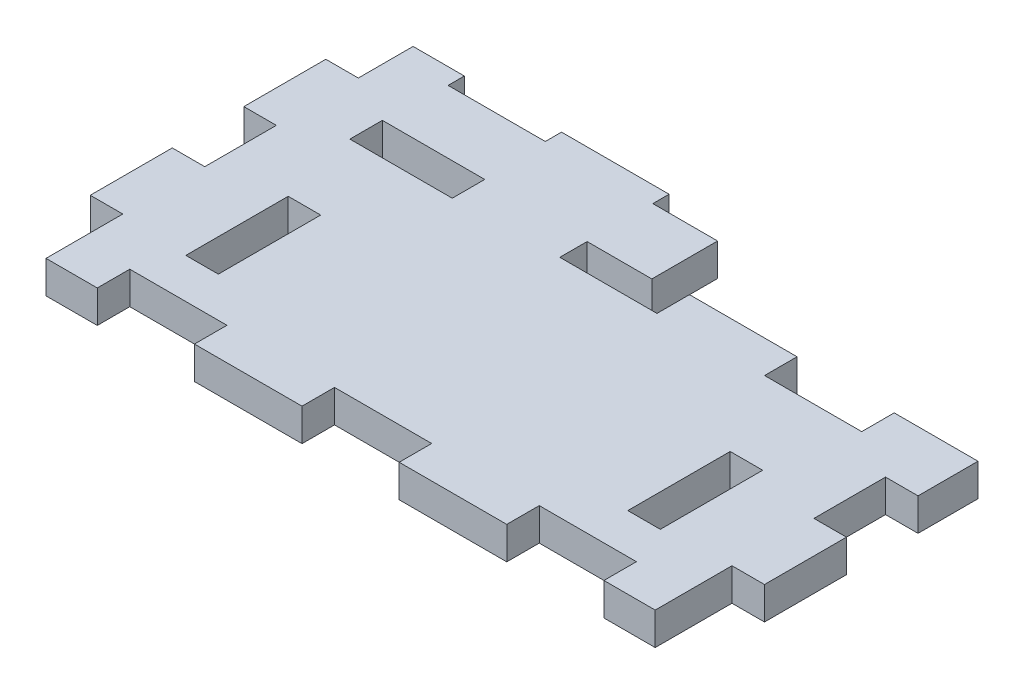
SolidWorks part; units mm, degrees
ref_plane "Front Plane" through (0, 0, 0) normal (0, 0, 1) x (1, 0, 0)
ref_plane "Top Plane" through (0, 0, 0) normal (0, 1, 0) x (1, 0, 0)
ref_plane "Right Plane" through (0, 0, 0) normal (1, 0, 0) x (0, 0, -1)
sketch "Sketch1" plane through (0, 0, 0) normal (0, 1, 0) x (1, 0, 0)
  line L1 (0, 0) -> (65.35, 0)
  line L2 (0, 0) -> (0, 35.35)
  line L3 (0, 35.35) -> (65.35, 35.35)
  line L4 (65.35, 0) -> (65.35, 35.35)
  dimension "D1" = 65.35
  dimension "D2" = 35.35
extrude "Boss-Extrude1" add sketch "Sketch1" along normal blind 3.175
sketch "Sketch2" plane through (0, 0, 0) normal (0, -1, 0) x (1, 0, 0)
  line L0 (65.35, -35.35) -> (0, -35.35) construction
  line L1 (65.35, -35.35) -> (37.175, -35.35)
  line L2 (65.35, -35.35) -> (65.35, -27.85)
  line L3 (65.35, -27.85) -> (37.175, -27.85)
  line L4 (37.175, -35.35) -> (37.175, -27.85)
  line L5 (65.35, 0) -> (65.35, -35.35) construction
  dimension "D1" = 7.5
  dimension "D2" = 28.175
extrude "Cut-Extrude1" cut sketch "Sketch2" against normal through all
sketch "Sketch3" plane through (0, 0, 0) normal (0, -1, 0) x (1, 0, 0)
  line L0 (0, 0) -> (65.35, 0) construction
  line L1 (62.175, -7.5) -> (65.35, -7.5)
  line L2 (62.175, -7.5) -> (62.175, 0)
  line L3 (62.175, 0) -> (65.35, 0)
  line L4 (65.35, -7.5) -> (65.35, 0)
  line L5 (0, -35.35) -> (0, 0) construction
  line L6 (57.675, -3.175) -> (47.675, -3.175)
  line L7 (57.675, -3.175) -> (57.675, 0)
  line L8 (57.675, 0) -> (47.675, 0)
  line L9 (47.675, -3.175) -> (47.675, 0)
  line L10 (37.675, -3.175) -> (27.675, -3.175)
  line L11 (37.675, -3.175) -> (37.675, 0)
  line L12 (37.675, 0) -> (27.675, 0)
  line L13 (27.675, -3.175) -> (27.675, 0)
  line L14 (17.675, -3.175) -> (7.675, -3.175)
  line L15 (17.675, -3.175) -> (17.675, 0)
  line L16 (17.675, 0) -> (7.675, 0)
  line L17 (7.675, -3.175) -> (7.675, 0)
  line L18 (3.175, -7.5) -> (0, -7.5)
  line L19 (3.175, -7.5) -> (3.175, 0)
  line L20 (3.175, 0) -> (0, 0)
  line L21 (0, -7.5) -> (0, 0)
  line L22 (37.175, -35.35) -> (0, -35.35) construction
  line L23 (3.175, -15) -> (0, -15)
  line L24 (3.175, -15) -> (3.175, -22.5)
  line L25 (3.175, -22.5) -> (0, -22.5)
  line L26 (0, -15) -> (0, -22.5)
  line L27 (3.175, -30) -> (0, -30)
  line L28 (3.175, -30) -> (3.175, -35.35)
  line L29 (3.175, -35.35) -> (0, -35.35)
  line L30 (0, -30) -> (0, -35.35)
  line L31 (7.675, -33.7625) -> (17.675, -33.7625)
  line L32 (7.675, -33.7625) -> (7.675, -35.35)
  line L33 (7.675, -35.35) -> (17.675, -35.35)
  line L34 (17.675, -33.7625) -> (17.675, -35.35)
  line L35 (65.35, -27.85) -> (37.175, -27.85) construction
  line L36 (17.675, -27.85) -> (7.675, -27.85)
  line L37 (17.675, -27.85) -> (17.675, -24.675)
  line L38 (17.675, -24.675) -> (7.675, -24.675)
  line L39 (7.675, -27.85) -> (7.675, -24.675)
  line L40 (27.675, -27.85) -> (37.675, -27.85)
  line L41 (27.675, -27.85) -> (27.675, -24.675)
  line L42 (27.675, -24.675) -> (37.675, -24.675)
  line L43 (37.675, -27.85) -> (37.675, -24.675)
  line L44 (34, -27.85) -> (37.175, -27.85)
  line L45 (34, -27.85) -> (34, -33.7625)
  line L46 (34, -33.7625) -> (37.175, -33.7625)
  line L47 (37.175, -27.85) -> (37.175, -33.7625)
  line L48 (27.675, -33.7625) -> (37.175, -33.7625)
  line L49 (27.675, -33.7625) -> (27.675, -35.35)
  line L50 (27.675, -35.35) -> (37.175, -35.35)
  line L51 (37.175, -33.7625) -> (37.175, -35.35)
  line L52 (47.675, -24.675) -> (57.675, -24.675)
  line L53 (47.675, -24.675) -> (47.675, -27.85)
  line L54 (47.675, -27.85) -> (57.675, -27.85)
  line L55 (57.675, -24.675) -> (57.675, -27.85)
  line L56 (65.35, 0) -> (65.35, -27.85) construction
  line L57 (62.175, -22.5) -> (65.35, -22.5)
  line L58 (62.175, -22.5) -> (62.175, -15)
  line L59 (62.175, -15) -> (65.35, -15)
  line L60 (65.35, -22.5) -> (65.35, -15)
  line L62 (37.175, -27.85) -> (37.175, -35.35) construction
  line M40 (37.175, -35.35) -> (37.175, -27.85)
  line M41 (37.175, -27.85) -> (65.35, -27.85)
  line M42 (65.35, -27.85) -> (65.35, 0)
  line M43 (65.35, 0) -> (0, 0)
  line M44 (0, 0) -> (0, -35.35)
  line M45 (0, -35.35) -> (37.175, -35.35)
  dimension "D1" = 10
  dimension "D2" = 10
  dimension "D3" = 10
  dimension "D4" = 10
  dimension "D5" = 10
  dimension "D6" = 4.5
  dimension "D7" = 3.175
  dimension "D8" = 7.5
  dimension "D9" = 7.5
  dimension "D10" = 5.35
  dimension "D11" = 7.5
  dimension "D12" = 7.5
  dimension "D13" = 5.9125
  dimension "D14" = 1.5875
extrude "Cut-Extrude2" cut sketch "Sketch3" against normal blind 3.175 contours L9 L6 L7 M43 | L2 L1 M42 M43 | L59 L58 L57 M42 | L55 L52 L53 M41 | L43 L42 L41 L40 M41 | L45 L46 L40 M40 | L48 L49 L46 M45 M40 | L39 L36 L37 L38 | L28 L27 M44 M45 | L25 L24 L23 M44 | L18 L19 M43 M44 | L17 L14 L15 M43 | L13 L10 L11 M43 | L33 L34 L31 L32
sketch "Sketch7" plane through (0, 0, 0) normal (0, -1, 0) x (1, 0, 0)
  line L1 (9.5, -16.825) -> (12.675, -16.825)
  line L2 (9.5, -16.825) -> (9.5, -6.825)
  line L3 (9.5, -6.825) -> (12.675, -6.825)
  line L4 (12.675, -16.825) -> (12.675, -6.825)
  line L5 (52.675, -16.825) -> (55.85, -16.825)
  line L6 (52.675, -16.825) -> (52.675, -6.825)
  line L7 (52.675, -6.825) -> (55.85, -6.825)
  line L8 (55.85, -16.825) -> (55.85, -6.825)
extrude "Cut-Extrude3" cut sketch "Sketch7" against normal through all
sketch "Sketch6" plane through (0, 3.175, 0) normal (0, 1, 0) x (1, 0, 0)
  line L60 (17.421, 27.596) -> (7.929, 27.596)
  line L61 (7.929, 27.596) -> (7.929, 24.929)
  line L62 (7.929, 24.929) -> (17.421, 24.929)
  line L63 (17.421, 24.929) -> (17.421, 27.596)
  line L64 (17.421, 27.596) -> (7.929, 27.596)
  line L65 (7.929, 27.596) -> (7.929, 24.929)
  line L66 (7.929, 24.929) -> (17.421, 24.929)
  line L67 (17.421, 24.929) -> (17.421, 27.596)
  line L92 (7.929, -0.254) -> (7.929, 2.921)
  line L93 (7.929, 2.921) -> (17.421, 2.921)
  line L94 (17.421, 2.921) -> (17.421, -0.254)
  line L95 (17.421, -0.254) -> (27.929, -0.254)
  line L96 (27.929, -0.254) -> (27.929, 2.921)
  line L97 (27.929, 2.921) -> (37.421, 2.921)
  line L98 (37.421, 2.921) -> (37.421, -0.254)
  line L99 (37.421, -0.254) -> (47.929, -0.254)
  line L100 (47.929, -0.254) -> (47.929, 2.921)
  line L101 (47.929, 2.921) -> (57.421, 2.921)
  line L102 (57.421, 2.921) -> (57.421, -0.254)
  line L103 (57.421, -0.254) -> (62.429, -0.254)
  line L104 (62.429, -0.254) -> (62.429, 7.246)
  line L105 (62.429, 7.246) -> (65.604, 7.246)
  line L106 (65.604, 7.246) -> (65.604, 15.254)
  line L107 (65.604, 15.254) -> (62.429, 15.254)
  line L108 (62.429, 15.254) -> (62.429, 22.246)
  line L109 (62.429, 22.246) -> (65.604, 22.246)
  line L110 (65.604, 22.246) -> (65.604, 28.104)
  line L111 (65.604, 28.104) -> (57.421, 28.104)
  line L112 (57.421, 28.104) -> (57.421, 24.929)
  line L113 (57.421, 24.929) -> (47.929, 24.929)
  line L114 (47.929, 24.929) -> (47.929, 28.104)
  line L115 (47.929, 28.104) -> (37.421, 28.104)
  line L116 (37.421, 28.104) -> (37.421, 24.929)
  line L117 (37.421, 24.929) -> (27.929, 24.929)
  line L118 (27.929, 24.929) -> (27.929, 27.596)
  line L119 (27.929, 27.596) -> (34.254, 27.596)
  line L120 (34.254, 27.596) -> (34.254, 34.0165)
  line L121 (34.254, 34.0165) -> (27.929, 34.0165)
  line L122 (27.929, 34.0165) -> (27.929, 35.604)
  line L123 (27.929, 35.604) -> (17.421, 35.604)
  line L124 (17.421, 35.604) -> (17.421, 34.0165)
  line L125 (17.421, 34.0165) -> (7.929, 34.0165)
  line L126 (7.929, 34.0165) -> (7.929, 35.604)
  line L127 (7.929, 35.604) -> (2.921, 35.604)
  line L128 (2.921, 35.604) -> (2.921, 30.254)
  line L129 (2.921, 30.254) -> (-0.254, 30.254)
  line L130 (-0.254, 30.254) -> (-0.254, 22.246)
  line L131 (-0.254, 22.246) -> (2.921, 22.246)
  line L132 (2.921, 22.246) -> (2.921, 15.254)
  line L133 (2.921, 15.254) -> (-0.254, 15.254)
  line L134 (-0.254, 15.254) -> (-0.254, 7.246)
  line L135 (-0.254, 7.246) -> (2.921, 7.246)
  line L136 (2.921, 7.246) -> (2.921, -0.254)
  line L137 (2.921, -0.254) -> (7.929, -0.254)
  line L138 (7.929, -0.254) -> (7.929, 2.921)
  line L139 (7.929, 2.921) -> (17.421, 2.921)
  line L140 (17.421, 2.921) -> (17.421, -0.254)
  line L141 (17.421, -0.254) -> (27.929, -0.254)
  line L142 (27.929, -0.254) -> (27.929, 2.921)
  line L143 (27.929, 2.921) -> (37.421, 2.921)
  line L144 (37.421, 2.921) -> (37.421, -0.254)
  line L145 (37.421, -0.254) -> (47.929, -0.254)
  line L146 (47.929, -0.254) -> (47.929, 2.921)
  line L147 (47.929, 2.921) -> (57.421, 2.921)
  line L148 (57.421, 2.921) -> (57.421, -0.254)
  line L149 (57.421, -0.254) -> (62.429, -0.254)
  line L150 (62.429, -0.254) -> (62.429, 7.246)
  line L151 (62.429, 7.246) -> (65.604, 7.246)
  line L152 (65.604, 7.246) -> (65.604, 15.254)
  line L153 (65.604, 15.254) -> (62.429, 15.254)
  line L154 (62.429, 15.254) -> (62.429, 22.246)
  line L155 (62.429, 22.246) -> (65.604, 22.246)
  line L156 (65.604, 22.246) -> (65.604, 28.104)
  line L157 (65.604, 28.104) -> (57.421, 28.104)
  line L158 (57.421, 28.104) -> (57.421, 24.929)
  line L159 (57.421, 24.929) -> (47.929, 24.929)
  line L160 (47.929, 24.929) -> (47.929, 28.104)
  line L161 (47.929, 28.104) -> (37.421, 28.104)
  line L162 (37.421, 28.104) -> (37.421, 24.929)
  line L163 (37.421, 24.929) -> (27.929, 24.929)
  line L164 (27.929, 24.929) -> (27.929, 27.596)
  line L165 (27.929, 27.596) -> (34.254, 27.596)
  line L166 (34.254, 27.596) -> (34.254, 34.0165)
  line L167 (34.254, 34.0165) -> (27.929, 34.0165)
  line L168 (27.929, 34.0165) -> (27.929, 35.604)
  line L169 (27.929, 35.604) -> (17.421, 35.604)
  line L170 (17.421, 35.604) -> (17.421, 34.0165)
  line L171 (17.421, 34.0165) -> (7.929, 34.0165)
  line L172 (7.929, 34.0165) -> (7.929, 35.604)
  line L173 (7.929, 35.604) -> (2.921, 35.604)
  line L174 (2.921, 35.604) -> (2.921, 30.254)
  line L175 (2.921, 30.254) -> (-0.254, 30.254)
  line L176 (-0.254, 30.254) -> (-0.254, 22.246)
  line L177 (-0.254, 22.246) -> (2.921, 22.246)
  line L178 (2.921, 22.246) -> (2.921, 15.254)
  line L179 (2.921, 15.254) -> (-0.254, 15.254)
  line L180 (-0.254, 15.254) -> (-0.254, 7.246)
  line L181 (-0.254, 7.246) -> (2.921, 7.246)
  line L182 (2.921, 7.246) -> (2.921, -0.254)
  line L183 (2.921, -0.254) -> (7.929, -0.254)
  line L192 (6.675, 4.175) -> (18.675, 4.175)
  line L193 (6.675, 1) -> (6.675, 4.175)
  line L194 (4.175, 1) -> (6.675, 1)
  line L195 (4.175, 8.5) -> (4.175, 1)
  line L196 (1, 8.5) -> (4.175, 8.5)
  line L197 (1, 14) -> (1, 8.5)
  line L198 (4.175, 14) -> (1, 14)
  line L199 (4.175, 23.5) -> (4.175, 14)
  line L200 (1, 23.5) -> (4.175, 23.5)
  line L201 (1, 29) -> (1, 23.5)
  line L202 (4.175, 29) -> (1, 29)
  line L203 (4.175, 34.35) -> (4.175, 29)
  line L204 (6.675, 34.35) -> (4.175, 34.35)
  line L205 (6.675, 32.7625) -> (6.675, 34.35)
  line L206 (18.675, 32.7625) -> (6.675, 32.7625)
  line L207 (18.675, 34.35) -> (18.675, 32.7625)
  line L208 (26.675, 34.35) -> (18.675, 34.35)
  line L209 (26.675, 32.7625) -> (26.675, 34.35)
  line L210 (33, 32.7625) -> (26.675, 32.7625)
  line L211 (33, 28.85) -> (33, 32.7625)
  line L212 (26.675, 28.85) -> (33, 28.85)
  line L213 (26.675, 23.675) -> (26.675, 28.85)
  line L214 (38.675, 23.675) -> (26.675, 23.675)
  line L215 (38.675, 26.85) -> (38.675, 23.675)
  line L216 (46.675, 26.85) -> (38.675, 26.85)
  line L217 (46.675, 23.675) -> (46.675, 26.85)
  line L218 (58.675, 23.675) -> (46.675, 23.675)
  line L219 (58.675, 26.85) -> (58.675, 23.675)
  line L220 (64.35, 26.85) -> (58.675, 26.85)
  line L221 (64.35, 23.5) -> (64.35, 26.85)
  line L222 (61.175, 23.5) -> (64.35, 23.5)
  line L223 (61.175, 14) -> (61.175, 23.5)
  line L224 (64.35, 14) -> (61.175, 14)
  line L225 (64.35, 8.5) -> (64.35, 14)
  line L226 (61.175, 8.5) -> (64.35, 8.5)
  line L227 (61.175, 1) -> (61.175, 8.5)
  line L228 (58.675, 1) -> (61.175, 1)
  line L229 (58.675, 4.175) -> (58.675, 1)
  line L230 (46.675, 4.175) -> (58.675, 4.175)
  line L231 (46.675, 1) -> (46.675, 4.175)
  line L232 (38.675, 1) -> (46.675, 1)
  line L233 (38.675, 4.175) -> (38.675, 1)
  line L234 (26.675, 4.175) -> (38.675, 4.175)
  line L235 (26.675, 1) -> (26.675, 4.175)
  line L236 (18.675, 1) -> (26.675, 1)
  line L237 (18.675, 4.175) -> (18.675, 1)
  line L238 (6.675, 4.175) -> (18.675, 4.175)
  line L239 (6.675, 1) -> (6.675, 4.175)
  line L240 (4.175, 1) -> (6.675, 1)
  line L241 (4.175, 8.5) -> (4.175, 1)
  line L242 (1, 8.5) -> (4.175, 8.5)
  line L243 (1, 14) -> (1, 8.5)
  line L244 (4.175, 14) -> (1, 14)
  line L245 (4.175, 23.5) -> (4.175, 14)
  line L246 (1, 23.5) -> (4.175, 23.5)
  line L247 (1, 29) -> (1, 23.5)
  line L248 (4.175, 29) -> (1, 29)
  line L249 (4.175, 34.35) -> (4.175, 29)
  line L250 (6.675, 34.35) -> (4.175, 34.35)
  line L251 (6.675, 32.7625) -> (6.675, 34.35)
  line L252 (18.675, 32.7625) -> (6.675, 32.7625)
  line L253 (18.675, 34.35) -> (18.675, 32.7625)
  line L254 (26.675, 34.35) -> (18.675, 34.35)
  line L255 (26.675, 32.7625) -> (26.675, 34.35)
  line L256 (33, 32.7625) -> (26.675, 32.7625)
  line L257 (33, 28.85) -> (33, 32.7625)
  line L258 (26.675, 28.85) -> (33, 28.85)
  line L259 (26.675, 23.675) -> (26.675, 28.85)
  line L260 (38.675, 23.675) -> (26.675, 23.675)
  line L261 (38.675, 26.85) -> (38.675, 23.675)
  line L262 (46.675, 26.85) -> (38.675, 26.85)
  line L263 (46.675, 23.675) -> (46.675, 26.85)
  line L264 (58.675, 23.675) -> (46.675, 23.675)
  line L265 (58.675, 26.85) -> (58.675, 23.675)
  line L266 (64.35, 26.85) -> (58.675, 26.85)
  line L267 (64.35, 23.5) -> (64.35, 26.85)
  line L268 (61.175, 23.5) -> (64.35, 23.5)
  line L269 (61.175, 14) -> (61.175, 23.5)
  line L270 (64.35, 14) -> (61.175, 14)
  line L271 (64.35, 8.5) -> (64.35, 14)
  line L272 (61.175, 8.5) -> (64.35, 8.5)
  line L273 (61.175, 1) -> (61.175, 8.5)
  line L274 (58.675, 1) -> (61.175, 1)
  line L275 (58.675, 4.175) -> (58.675, 1)
  line L276 (46.675, 4.175) -> (58.675, 4.175)
  line L277 (46.675, 1) -> (46.675, 4.175)
  line L278 (38.675, 1) -> (46.675, 1)
  line L279 (38.675, 4.175) -> (38.675, 1)
  line L280 (26.675, 4.175) -> (38.675, 4.175)
  line L281 (26.675, 1) -> (26.675, 4.175)
  line L282 (18.675, 1) -> (26.675, 1)
  line L283 (18.675, 4.175) -> (18.675, 1)
  dimension "D1" = 0.254
  dimension "D2" = 0.254
  dimension "D3" = 1
extrude "Boss-Extrude2" add sketch "Sketch6" against normal blind 3.175 contours L182 L183 L138 L139 L140 L141 L142 L143 L144 L145 L146 L147 L148 L149 L150 L151 L152 L153 L154 L155 L156 L157 L158 L159 L160 L161 L162 L163 L164 L165 L166 L167 L168 L169 L170 L171 L172 L173 L174 L175 L176 L177 L178 L179 L180 L181 L283 L238 L239 L240
